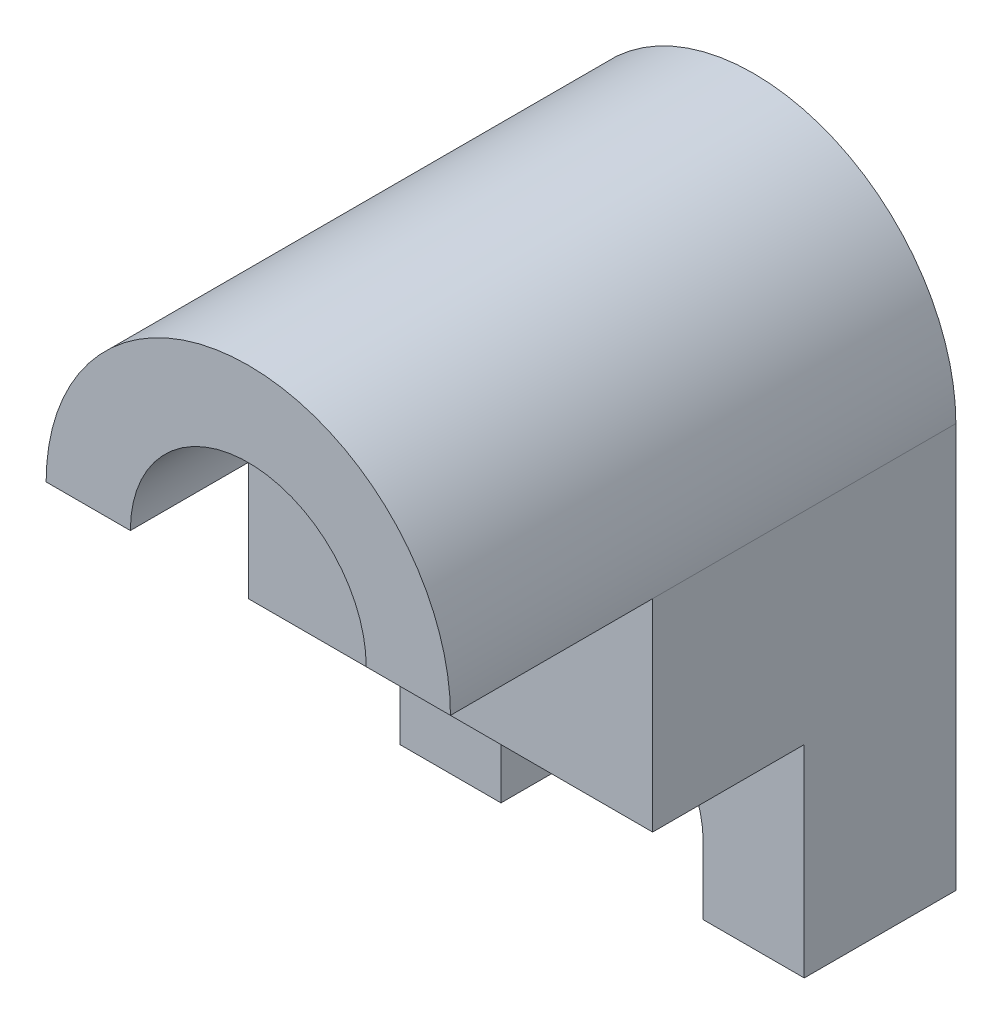
SolidWorks part; units mm, degrees
ref_plane "Front" through (0, 0, 0) normal (0, 0, 1) x (1, 0, 0)
ref_plane "Top" through (0, 0, 0) normal (0, 1, 0) x (1, 0, 0)
ref_plane "Right" through (0, 0, 0) normal (1, 0, 0) x (0, 0, -1)
sketch "Sketch1" plane through (0, 0, 0) normal (0, 0, 1) x (1, 0, 0)
  line L0 (0, -6) -> (0, -3.9962) construction
  line L1 (-6, -6) -> (6, -6)
  line L2 (-6, -6) -> (-6, 6)
  line L4 (6, -6) -> (6, 6)
  line L5 (-3, -6) -> (-3, -3.9962)
  line L6 (3, -6) -> (3, -3.9962)
  arc A0 (-6, 6) -> (6, 6) centre (0, 6) cw
  circle A1 centre (0, 6) radius 3.5
  arc A2 (-3, -6) -> (3, -6) centre (0, -6) ccw
  arc A3 (3, -3.9962) -> (-3, -3.9962) centre (0, -3.9962) ccw
  point P0 (0, 0)
  point P10 (0, -4.9981)
  dimension "D3" = 7
  dimension "D4" = 3
  dimension "D1" = 12
  dimension "D2" = 12
extrude "Boss-Extrude1" add sketch "Sketch1" along normal blind 15 contours A3 L6 L1 L4 A0 L2 L5 A1
sketch "Sketch2" plane through (-6, 0, 0) normal (-1, 0, 0) x (0, 0, 1)
  line L0 (4.5, -6) -> (4.5, 0)
  line L1 (15, -6) -> (0, -6) construction
  line L2 (4.5, 0) -> (9, 0)
  line L3 (9, 0) -> (9, 6)
  line L4 (15, 6) -> (0, 6) construction
  line L5 (9, 6) -> (15, 6)
  line L6 (15, 6) -> (15, -6)
  line L7 (15, -6) -> (4.5, -6)
  dimension "D1" = 10.5
  dimension "D2" = 6
  dimension "D3" = 6
extrude "Cut-Extrude1" cut sketch "Sketch2" against normal blind 15
